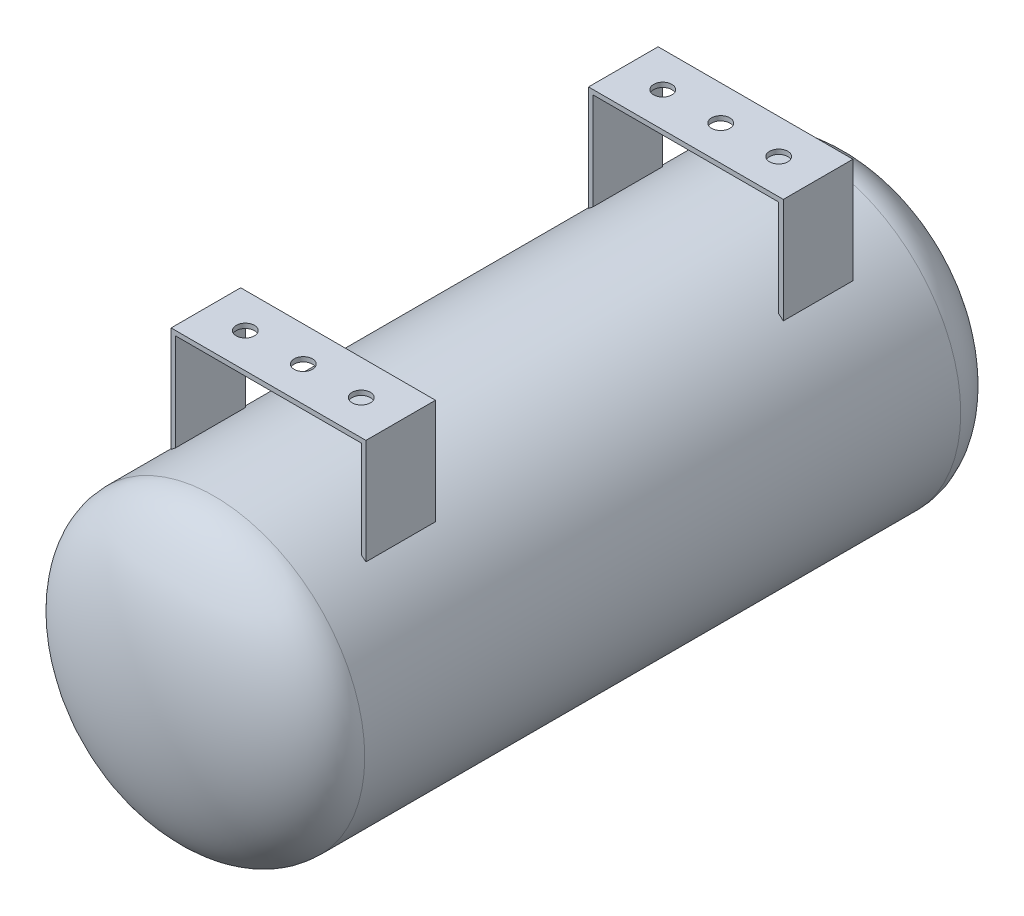
SolidWorks part; units mm, degrees
ref_plane "Front Plane" through (0, 0, 0) normal (0, 0, 1) x (1, 0, 0)
ref_plane "Top Plane" through (0, 0, 0) normal (0, 1, 0) x (1, 0, 0)
ref_plane "Right Plane" through (0, 0, 0) normal (1, 0, 0) x (0, 0, -1)
sketch "Sketch4" plane through (0, 0, 0) normal (0, 1, 0) x (1, 0, 0)
  line L0 (-82.55, -163.195) -> (-82.55, 163.195)
  line L1 (0, -55) -> (0, 55) construction
  line L2 (-55, 0) -> (55, 0) construction
  line L3 (0, 0) -> (0, 203.835) construction
  line L4 (0, 203.835) -> (0, -203.835)
  ellipse E0 centre (0, 163.195) end of major axis (-82.55, 163.195) minor radius 40.64 (0, 203.835) -> (-82.55, 163.195) ccw
  ellipse E1 centre (0, -163.195) end of major axis (-82.55, -163.195) minor radius 40.64 (0, -203.835) -> (-82.55, -163.195) cw
  point P3 (-82.55, 0)
  dimension "D1" = 82.55
  dimension "D2" = 326.39
  dimension "D3" = 40.64
revolve "Revolve1" add sketch "Sketch4" angle 360 about L3
ref_plane "Plane1" through (0, 120.65, 0) normal (0, 1, 0) x (1, 0, 0)
sketch "Sketch6" plane through (0, 120.65, 0) normal (0, 1, 0) x (1, 0, 0)
  line L0 (0, -90.805) -> (0, 90.805) construction
  line L1 (-53.34, 133.35) -> (53.34, 133.35)
  line L2 (-53.34, 133.35) -> (-53.34, 95.25)
  line L3 (-53.34, 95.25) -> (53.34, 95.25)
  line L4 (53.34, 133.35) -> (53.34, 95.25)
  line L5 (-90.805, 0) -> (90.805, 0) construction
  line L6 (53.34, -133.35) -> (53.34, -95.25)
  line L7 (-53.34, -95.25) -> (53.34, -95.25)
  line L8 (-53.34, -133.35) -> (-53.34, -95.25)
  line L9 (-53.34, -133.35) -> (53.34, -133.35)
  circle A0 centre (-31.75, 114.3) radius 5
  circle A1 centre (0, 114.3) radius 5
  circle A2 centre (31.75, 114.3) radius 5
  circle A3 centre (31.75, -114.3) radius 5
  circle A4 centre (0, -114.3) radius 5
  circle A5 centre (-31.75, -114.3) radius 5
  point P4 (0, 133.35)
  point P7 (-53.34, 114.3)
  point P16 (0, 95.25)
  dimension "D4" = 10
  dimension "D5" = 10
  dimension "D6" = 10
  dimension "D1" = 106.68
  dimension "D2" = 38.1
  dimension "D3" = 114.3
  dimension "D8" = 31.75
  dimension "D9" = 31.75
extrude "Boss-Extrude1" add sketch "Sketch6" against normal blind 2.54 separate body
sketch "Sketch7" plane through (0, 120.65, 0) normal (0, 1, 0) x (1, 0, 0)
  line L0 (-53.34, 95.25) -> (53.34, 95.25) construction
  line L1 (-53.34, 133.35) -> (-50.8, 133.35)
  line L2 (-53.34, 133.35) -> (-53.34, 95.25)
  line L3 (-53.34, 95.25) -> (-50.8, 95.25)
  line L4 (-50.8, 133.35) -> (-50.8, 95.25)
  line L5 (0, -111.76) -> (0, 111.76) construction
  line L6 (53.34, 95.25) -> (50.8, 95.25)
  line L7 (53.34, 133.35) -> (50.8, 133.35)
  line L8 (53.34, 133.35) -> (53.34, 95.25)
  line L9 (50.8, 133.35) -> (50.8, 95.25)
  line L10 (-90.805, 0) -> (90.805, 0) construction
  line L11 (50.8, -133.35) -> (50.8, -95.25)
  line L12 (53.34, -133.35) -> (53.34, -95.25)
  line L13 (53.34, -133.35) -> (50.8, -133.35)
  line L14 (53.34, -95.25) -> (50.8, -95.25)
  line L15 (-50.8, -133.35) -> (-50.8, -95.25)
  line L16 (-53.34, -95.25) -> (-50.8, -95.25)
  line L17 (-53.34, -133.35) -> (-53.34, -95.25)
  line L18 (-53.34, -133.35) -> (-50.8, -133.35)
  dimension "D1" = 2.54
extrude "Boss-Extrude2" add sketch "Sketch7" against normal up to surface (55.5819 mm away)
equation "\"D5@Sketch6\"=\"D4@Sketch6\""
equation "\"D6@Sketch6\"=\"D5@Sketch6\""
